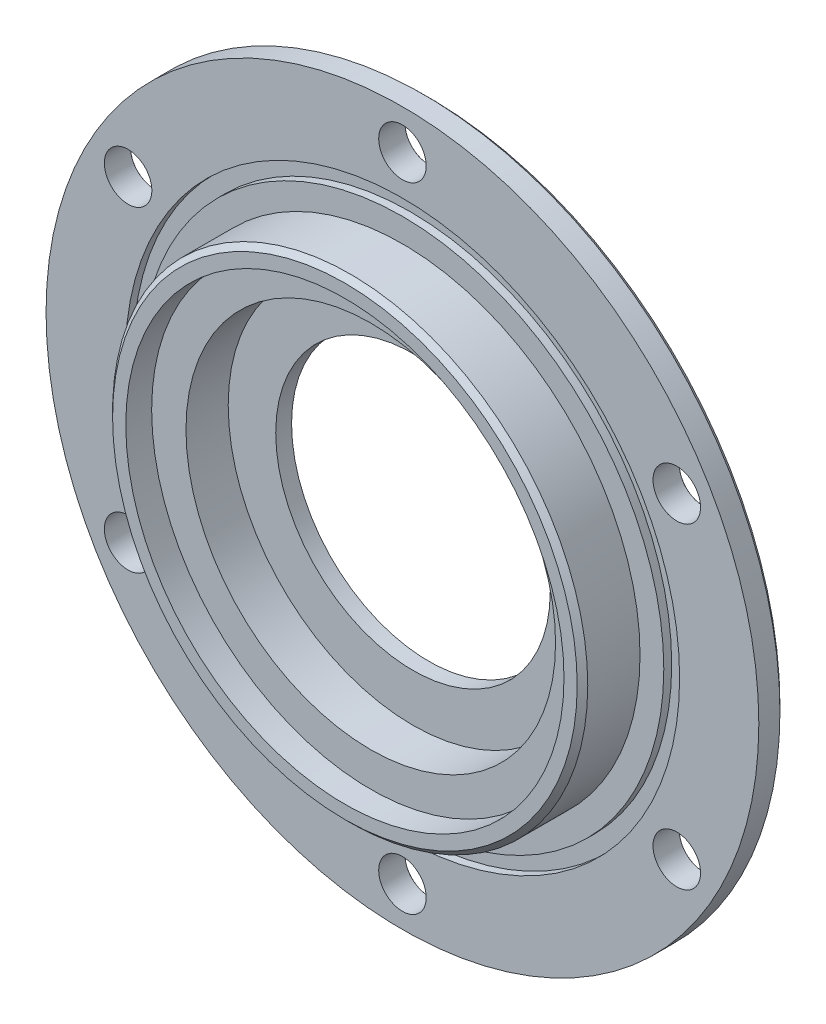
SolidWorks part; units mm, degrees
material "6061-T6 (SS)"
ref_plane "Piano frontale" through (0, 0, 0) normal (0, 0, 1) x (1, 0, 0)
ref_plane "Piano superiore" through (0, 0, 0) normal (0, 1, 0) x (1, 0, 0)
ref_plane "Piano destro" through (0, 0, 0) normal (1, 0, 0) x (0, 0, -1)
sketch "Schizzo2" plane through (0, 0, 0) normal (0, 0, 1) x (1, 0, 0)
  circle A0 centre (0, 0) radius 67.5
  dimension "D1" = 135
extrude "Estrusione-Estrusione1" add sketch "Schizzo2" along normal blind 5
sketch "Schizzo3" plane through (0, 0, 5) normal (0, 0, 1) x (1, 0, 0)
  circle A0 centre (0, 0) radius 45
  point P0 (0, 0)
  dimension "D1" = 90
extrude "Estrusione-Estrusione2" add sketch "Schizzo3" along normal blind 6
sketch "Schizzo4" plane through (0, 0, 0) normal (0, 0, -1) x (-1, 0, 0)
  circle A0 centre (0, 0) radius 26
  dimension "D1" = 52
extrude "Taglio-Estrusione1" cut sketch "Schizzo4" against normal blind 3
sketch "Schizzo5" plane through (0, 0, 3) normal (0, 0, -1) x (-1, 0, 0)
  circle A0 centre (0, 0) radius 35
  dimension "D1" = 70
extrude "Taglio-Estrusione2" cut sketch "Schizzo5" against normal through all
chamfer "Smusso1" distance 1 angle 45 1 edges at (67.5, 0, 0)
sketch "Schizzo6" plane through (0, 0, 0) normal (0, 0, -1) x (-1, 0, 0)
  point P0 (0, 60)
  dimension "D1" = 60
hole_wizard "Foro per Vite M8-1" positions "Schizzo7" profile "Schizzo8" hole size "M8" standard "ISO" end condition through all
sketch "Schizzo7" plane through (0, 0, 0) normal (0, 0, -1) x (-1, 0, 0)
  point P0 (0, 60)
sketch "Schizzo8" plane through (0, 60, 0) normal (1, 0, 0) x (0, 1, 0)
  line L0 (0, 0) -> (0, 11)
  line L1 (0, 11) -> (4.5, 11)
  line L2 (4.5, 11) -> (4.5, 0.025)
  line L3 (4.5, 0.025) -> (4.525, 0)
  line L5 (4.525, 0) -> (0, 0)
  line L6 (-4.5, 0.025) -> (-4.525, 0) construction
  line L11 (0, -6.35) -> (0, 107.95) construction
  dimension "Thru Hole Dia." = 9
  dimension "Thru Hole Depth" = 11
  dimension "Near C'Sink Dia." = 9.05
  dimension "Near C'Sink Angle" = 90
pattern_circular "RipetizioneCircolare1" count 6 over 360 about axis through (0, 0, 0) along (0, 0, 1) of "Foro per Vite M8-1"
sketch "Schizzo9" plane through (0, 0, 5) normal (0, 0, 1) x (1, 0, 0)
  circle A0 centre (0, 0) radius 49.5
  circle A1 centre (0, 0) radius 52.5
  dimension "D1" = 99
  dimension "D2" = 105
extrude "Taglio-Estrusione3" cut sketch "Schizzo9" against normal blind 1.5
sketch "Schizzo10" plane through (0, 0, 11) normal (0, 0, 1) x (1, 0, 0)
  circle A0 centre (0, 0) radius 41.5
  circle A1 centre (0, 0) radius 45 construction
  circle A2 centre (0, 0) radius 45
  dimension "D1" = 83
extrude "Estrusione-Estrusione3" add sketch "Schizzo10" along normal blind 4.9
chamfer "Smusso2" distance 1 angle 45 1 edges at (45, 0, 15.9)
